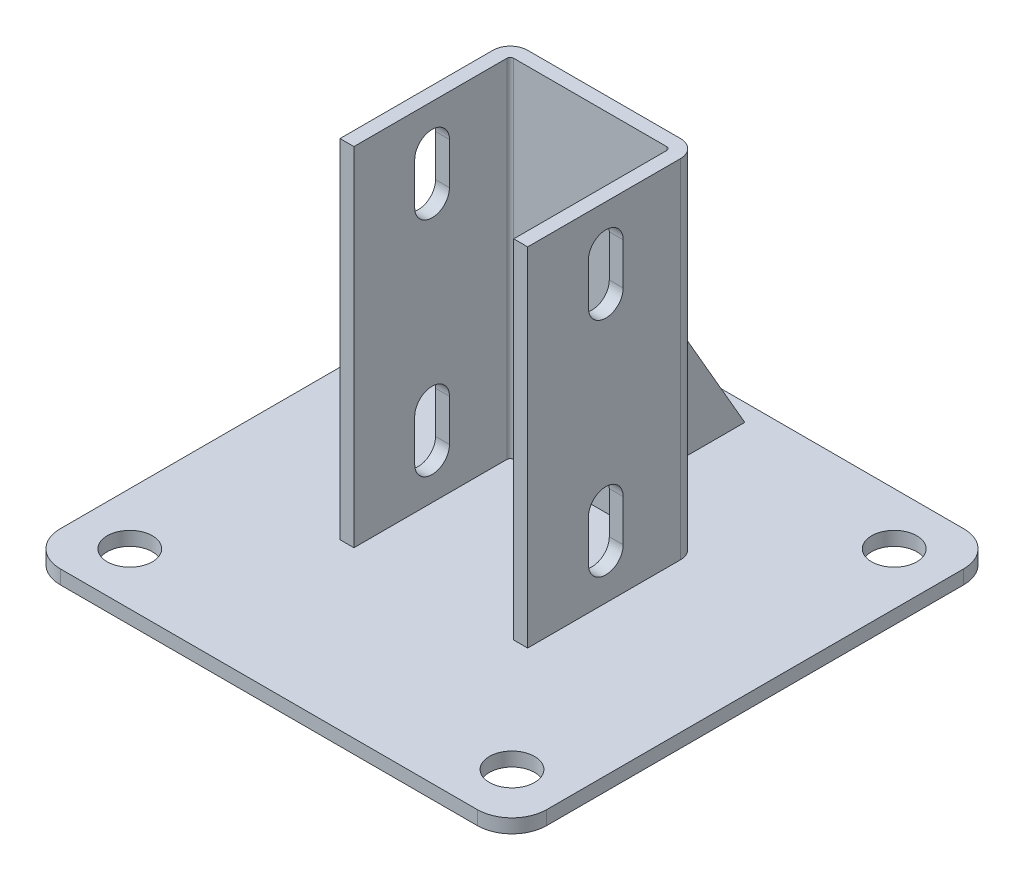
SolidWorks part; units mm, degrees
material "Ст3пс ГОСТ 380-2005"
ref_plane "Спереди" through (0, 0, 0) normal (0, 0, 1) x (1, 0, 0)
ref_plane "Сверху" through (0, 0, 0) normal (0, 1, 0) x (1, 0, 0)
ref_plane "Справа" through (0, 0, 0) normal (1, 0, 0) x (0, 0, -1)
sketch "Эскиз2" plane through (0, 0, 0) normal (0, 1, 0) x (1, 0, 0)
  line L1 (-70, -70) -> (70, -70)
  line L2 (-70, -70) -> (-70, 70)
  line L3 (-70, 70) -> (70, 70)
  line L4 (70, -70) -> (70, 70)
  line L5 (-70, -70) -> (70, 70) construction
  line L6 (-70, 70) -> (70, -70) construction
  point P0 (0, 0)
  dimension "D1" = 140
extrude "Бобышка-Вытянуть1" add sketch "Эскиз2" along normal blind 4
sketch "Эскиз3" plane through (0, 4, 0) normal (0, 1, 0) x (1, 0, 0)
  line L0 (-23, -22.5) -> (-23, 22.5)
  line L1 (-23, 22.5) -> (23, 22.5)
  line L2 (23, 22.5) -> (23, -22.5)
  point P2 (0, 22.5)
  point P5 (-23, 0)
  dimension "D2" = 46
  dimension "D3" = 45
extrude "Вытянуть-Тонкостенный1" add sketch "Эскиз3" along normal offset from surface (100 mm away) 104 thin up to face at (0, 0, 0) thin type one direction reverse wall 4
sketch "Эскиз4" plane through (0, 0, 0) normal (1, 0, 0) x (0, 0, -1)
  line L0 (26.5, 70.684) -> (65, 4)
  line L1 (26.5, 104) -> (26.5, 4) construction
  line L2 (-70, 4) -> (70, 4) construction
  line L3 (65, 4) -> (26.5, 4)
  line L4 (26.5, 4) -> (26.5, 70.684)
  line L5 (70, 4) -> (70, 0) construction
  dimension "D1" = 30
  dimension "D2" = 5
extrude "Бобышка-Вытянуть2" add sketch "Эскиз4" along normal mid plane 4
sketch "Эскиз5" plane through (27, 0, 0) normal (1, 0, 0) x (0, 0, -1)
  line L0 (0, 92) -> (0, 80) construction
  line L1 (5, 92) -> (5, 80)
  line L2 (-5, 92) -> (-5, 80)
  line L3 (0, 28) -> (0, 16) construction
  line L4 (5, 28) -> (5, 16)
  line L5 (-5, 28) -> (-5, 16)
  line L6 (-22.5, 104) -> (21.5, 104) construction
  line L7 (-70, 4) -> (70, 4) construction
  arc A0 (5, 92) -> (-5, 92) centre (0, 92) ccw
  arc A1 (-5, 80) -> (5, 80) centre (0, 80) ccw
  arc A2 (5, 28) -> (-5, 28) centre (0, 28) ccw
  arc A3 (-5, 16) -> (5, 16) centre (0, 16) ccw
  point P3 (0, 86)
  point P8 (0, 22)
  dimension "D2" = 12
  dimension "D4" = 12
  dimension "D1" = 10
  dimension "D3" = 12
extrude "Вырез-Вытянуть1" cut sketch "Эскиз5" against normal through all
sketch "Эскиз6" plane through (0, 4, 0) normal (0, 1, 0) x (1, 0, 0)
  line L0 (-70, 70) -> (-70, -70) construction
  line L1 (55, -55) -> (-55, -55) construction
  line L2 (55, -55) -> (55, 55) construction
  line L3 (55, 55) -> (-55, 55) construction
  line L4 (-55, -55) -> (-55, 55) construction
  line L5 (55, -55) -> (-55, 55) construction
  line L6 (55, 55) -> (-55, -55) construction
  line L7 (70, 70) -> (-70, 70) construction
  circle A0 centre (-55, 55) radius 6.5
  circle A1 centre (-55, -55) radius 6.5
  circle A2 centre (55, 55) radius 6.5
  circle A3 centre (55, -55) radius 6.5
  point P0 (0, 0)
  dimension "D1" = 13
  dimension "D2" = 15
  dimension "D3" = 15
extrude "Вырез-Вытянуть2" cut sketch "Эскиз6" against normal through all
fillet "Скругление1" radius 10 4 edges at (70, 2, 70) (-70, 2, 70) (-70, 2, -70) (70, 2, -70)
